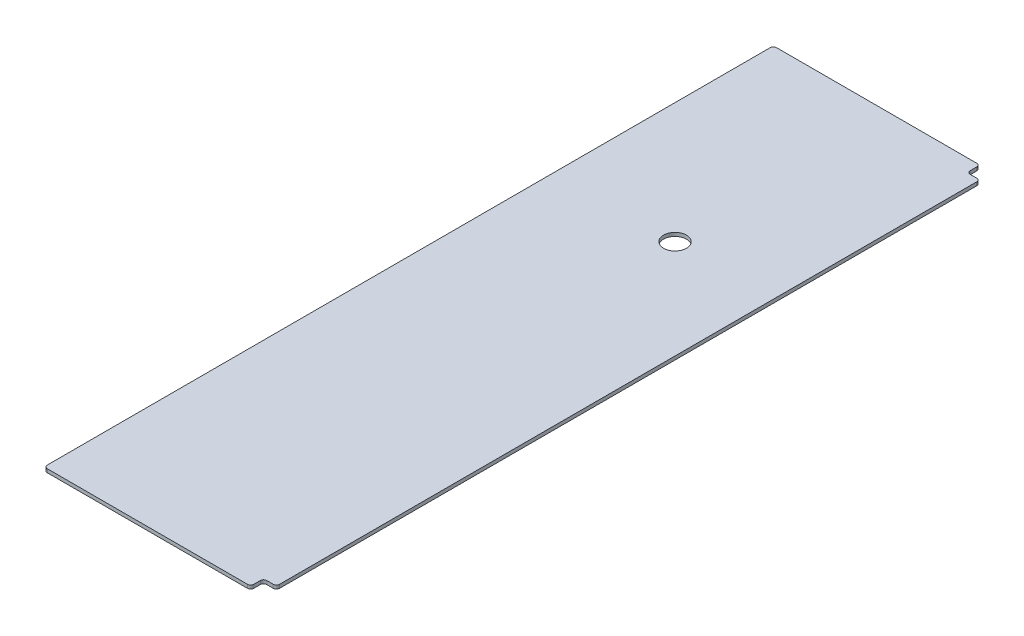
SolidWorks part; units mm, degrees
ref_plane "Front Plane" through (0, 0, 0) normal (0, 0, 1) x (1, 0, 0)
ref_plane "Top Plane" through (0, 0, 0) normal (0, 1, 0) x (1, 0, 0)
ref_plane "Right Plane" through (0, 0, 0) normal (1, 0, 0) x (0, 0, -1)
sketch "Sketch1" plane through (0, 0, 0) normal (0, 1, 0) x (1, 0, 0)
  line L1 (0, 0) -> (190.5, 0)
  line L2 (0, 0) -> (0, 609.6)
  line L3 (0, 609.6) -> (190.5, 609.6)
  line L4 (190.5, 0) -> (190.5, 609.6)
  dimension "D1" = 609.6
  dimension "D2" = 190.5
extrude "Boss-Extrude1" add sketch "Sketch1" along normal blind 2.7781
sketch "Sketch2" plane through (0, 2.7781, 0) normal (0, 1, 0) x (1, 0, 0)
  line L0 (190.5, 0) -> (190.5, 609.6) construction
  line L1 (0, 0) -> (190.5, 0)
  line L2 (0, 0) -> (0, 17.78)
  line L3 (0, 17.78) -> (190.5, 17.78)
  line L4 (190.5, 0) -> (190.5, 17.78)
  line L6 (0, 609.6) -> (190.5, 609.6)
  line L7 (0, 609.6) -> (0, 591.82)
  line L8 (0, 591.82) -> (190.5, 591.82)
  line L9 (190.5, 609.6) -> (190.5, 591.82)
  dimension "D1" = 17.78
  dimension "D2" = 17.78
extrude "Cut-Extrude1" cut sketch "Sketch2" against normal through all
sketch "Sketch3" plane through (0, 2.7781, 0) normal (0, 1, 0) x (1, 0, 0)
  line L0 (190.5, 17.78) -> (0, 17.78) construction
  line L1 (0, 591.82) -> (17.78, 591.82)
  line L2 (0, 591.82) -> (0, 17.78)
  line L3 (0, 17.78) -> (17.78, 17.78)
  line L4 (17.78, 591.82) -> (17.78, 17.78)
  dimension "D1" = 17.78
extrude "Cut-Extrude2" cut sketch "Sketch3" against normal through all
sketch "Sketch4" plane through (0, 2.7781, 0) normal (0, 1, 0) x (1, 0, 0)
  line L16 (190.5, 591.82) -> (180.34, 591.82)
  line L17 (190.5, 591.82) -> (190.5, 581.66)
  line L18 (190.5, 581.66) -> (180.34, 581.66)
  line L19 (180.34, 591.82) -> (180.34, 581.66)
  line L20 (190.5, 17.78) -> (180.34, 17.78)
  line L21 (190.5, 17.78) -> (190.5, 27.94)
  line L22 (190.5, 27.94) -> (180.34, 27.94)
  line L23 (180.34, 17.78) -> (180.34, 27.94)
  dimension "D4" = 10.16
extrude "Cut-Extrude3" cut sketch "Sketch4" against normal through all
fillet "Fillet1" radius 2.54 8 edges at (180.34, 1.3891, -591.82) (190.5, 1.3891, -581.66) (190.5, 1.3891, -27.94) (180.34, 1.3891, -17.78) (180.34, 1.3891, -27.94) (180.34, 1.3891, -581.66) (17.78, 1.3891, -591.82) (17.78, 1.3891, -17.78)
sketch "Sketch5" plane through (0, 0, 0) normal (0, -1, 0) x (1, 0, 0)
  circle A0 centre (112.58, -419.6) radius 9
  circle A1 centre (112.58, -419.6) radius 10.78 construction
  dimension "D1" = 18
extrude "Cut-Extrude4" cut sketch "Sketch5" against normal through all
